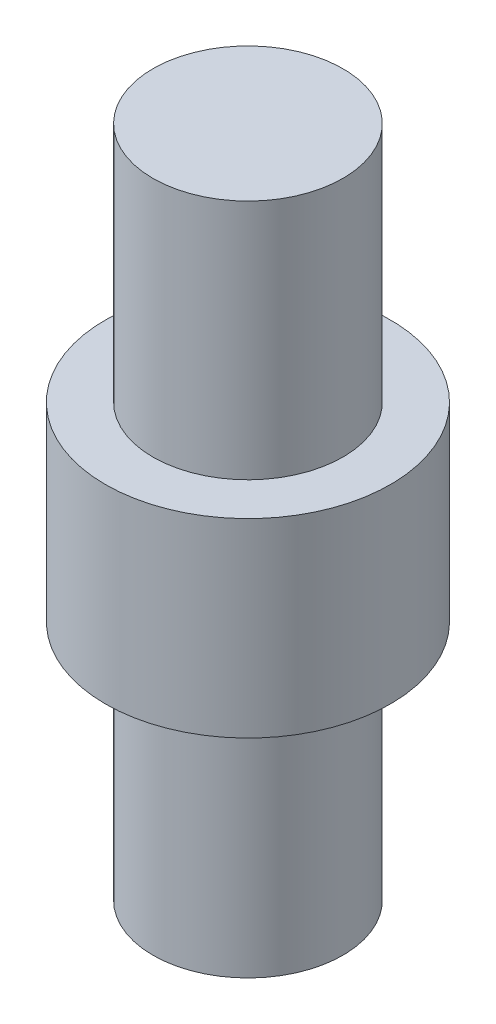
SolidWorks part; units mm, degrees
material "Nylon 101"
ref_plane "Front Plane" through (0, 0, 0) normal (0, 0, 1) x (1, 0, 0)
ref_plane "Top Plane" through (0, 0, 0) normal (0, 1, 0) x (1, 0, 0)
ref_plane "Right Plane" through (0, 0, 0) normal (1, 0, 0) x (0, 0, -1)
sketch "Sketch1" plane through (0, 0, 0) normal (0, 1, 0) x (1, 0, 0)
  circle A0 centre (0, 0) radius 1.5
  dimension "D1" = 3
extrude "Boss-Extrude1" add sketch "Sketch1" along normal mid plane 2
sketch "Sketch2" plane through (0, 1, 0) normal (0, 1, 0) x (1, 0, 0)
  circle A0 centre (0, 0) radius 1
  dimension "D1" = 2
extrude "Boss-Extrude2" add sketch "Sketch2" along normal blind 2.54
mirror "Mirror1" about plane through (0, 0, 0) normal (0, 1, 0) of "Boss-Extrude2"
